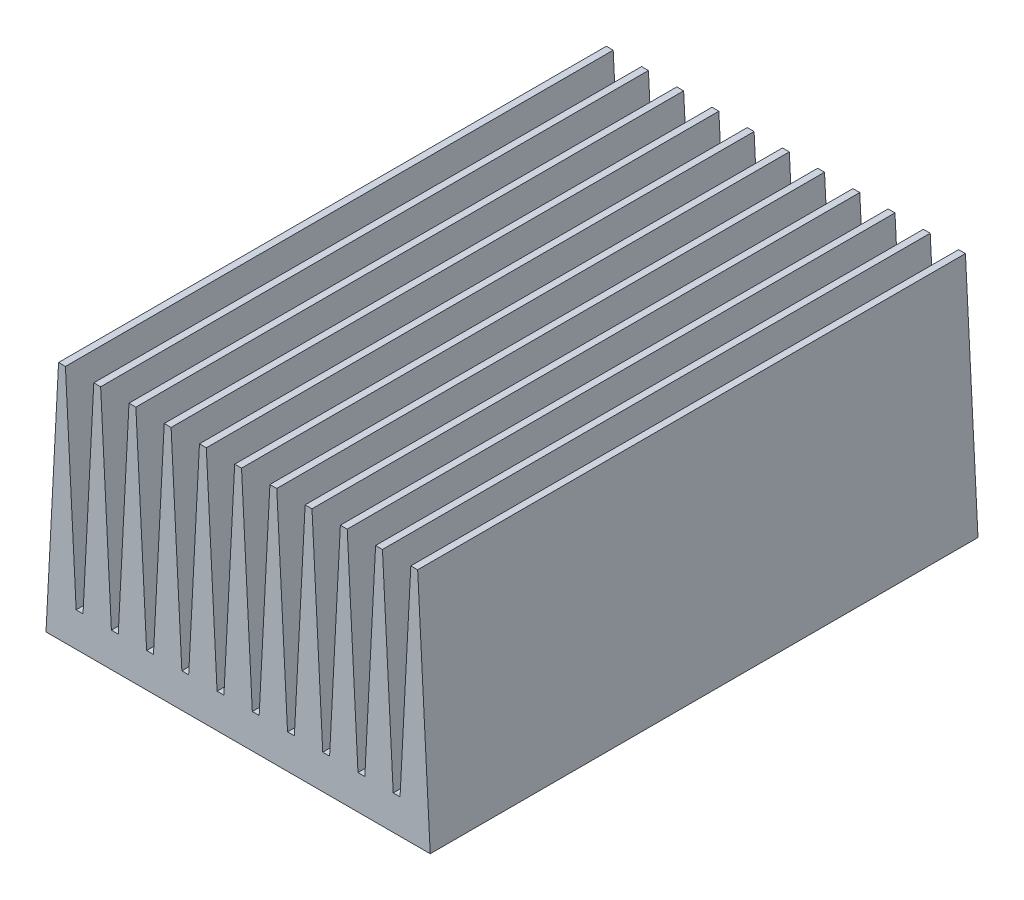
SolidWorks part; units mm, degrees
ref_plane "Front Plane" through (0, 0, 0) normal (0, 0, 1) x (1, 0, 0)
ref_plane "Top Plane" through (0, 0, 0) normal (0, 1, 0) x (1, 0, 0)
ref_plane "Right Plane" through (0, 0, 0) normal (1, 0, 0) x (0, 0, -1)
sketch "Sketch1" plane through (0, 0, 0) normal (0, 0, 1) x (1, 0, 0)
  line L0 (0, 0) -> (13.7019, 0)
  line L1 (13.7019, 0) -> (-24.2575, 0)
  line L2 (13.7019, 0) -> (11.8676, 35)
  line L3 (11.8676, 35) -> (10.8676, 35)
  line L4 (10.8676, 35) -> (9.2954, 5)
  line L5 (9.2954, 5) -> (8.2954, 5)
  line L6 (8.2954, 5) -> (6.7231, 35)
  line L7 (6.7231, 35) -> (5.7231, 35)
  line L8 (5.7231, 35) -> (4.1509, 5)
  line L9 (3.1509, 5) -> (1.5787, 35)
  line L10 (1.5787, 35) -> (0.5787, 35)
  line L11 (0.5787, 35) -> (-0.9936, 5)
  line L12 (-1.9936, 5) -> (-3.5658, 35)
  line L13 (-3.5658, 35) -> (-4.5658, 35)
  line L14 (-4.5658, 35) -> (-6.138, 5)
  line L15 (-7.138, 5) -> (-8.7103, 35)
  line L16 (-8.7103, 35) -> (-9.7103, 35)
  line L17 (-9.7103, 35) -> (-11.2825, 5)
  line L18 (-12.2825, 5) -> (-13.8547, 35)
  line L19 (-13.8547, 35) -> (-14.8547, 35)
  line L20 (-14.8547, 35) -> (-16.427, 5)
  line L21 (-17.427, 5) -> (-18.9992, 35)
  line L22 (-18.9992, 35) -> (-19.9992, 35)
  line L23 (-19.9992, 35) -> (-21.5714, 5)
  line L24 (-22.5714, 5) -> (-24.1437, 35)
  line L25 (-24.1437, 35) -> (-25.1437, 35)
  line L26 (-25.1437, 35) -> (-26.7159, 5)
  line L27 (-27.7159, 5) -> (-29.2881, 35)
  line L28 (-29.2881, 35) -> (-30.2881, 35)
  line L29 (-30.2881, 35) -> (-31.8604, 5)
  line L30 (-32.8604, 5) -> (-34.4326, 35)
  line L31 (-34.4326, 35) -> (-35.4326, 35)
  line L32 (-35.4326, 35) -> (-37.0048, 5)
  line L33 (-38.0048, 5) -> (-39.5771, 35)
  line L34 (-39.5771, 35) -> (-40.5771, 35)
  line L35 (-40.5771, 35) -> (-42.1493, 5)
  line L36 (4.1509, 5) -> (3.1509, 5)
  line L37 (-38.0048, 5) -> (-37.0048, 5)
  line L38 (-32.8604, 5) -> (-31.8604, 5)
  line L39 (-27.7159, 5) -> (-26.7159, 5)
  line L40 (-22.5714, 5) -> (-21.5714, 5)
  line L41 (-16.427, 5) -> (-17.427, 5)
  line L42 (-12.2825, 5) -> (-11.2825, 5)
  line L43 (-7.138, 5) -> (-6.138, 5)
  line L44 (-1.9936, 5) -> (-0.9936, 5)
  line L45 (0, 0) -> (-42.4113, 0)
  line L46 (-42.1493, 5) -> (-42.4113, 0)
  point P3 (8.7954, 5)
  point P12 (13.4398, 5)
  dimension "D1" = 5
  dimension "D2" = 87
  dimension "D3" = 1
  dimension "D4" = 1
  dimension "D5" = 35
  dimension "D6" = 93
  dimension "D7" = 35
  dimension "D8" = 93
  dimension "D9" = 1
  dimension "D10" = 93
  dimension "D11" = 5.1445
  dimension "D12" = 10
extrude "Boss-Extrude1" add sketch "Sketch1" along normal blind 80 contours L35 L46 L45 L1 L0 L2 L3 L4 L5 L6 L7 L8 L36 L9 L10 L11 L44 L12 L13 L14 L43 L15 L16 L17 L42 L18 L19 L20 L41 L21 L22 L23 L40 L24 L25 L26 L39 L27 L28 L29 L38 L30 L31 L32 L37 L33 L34
